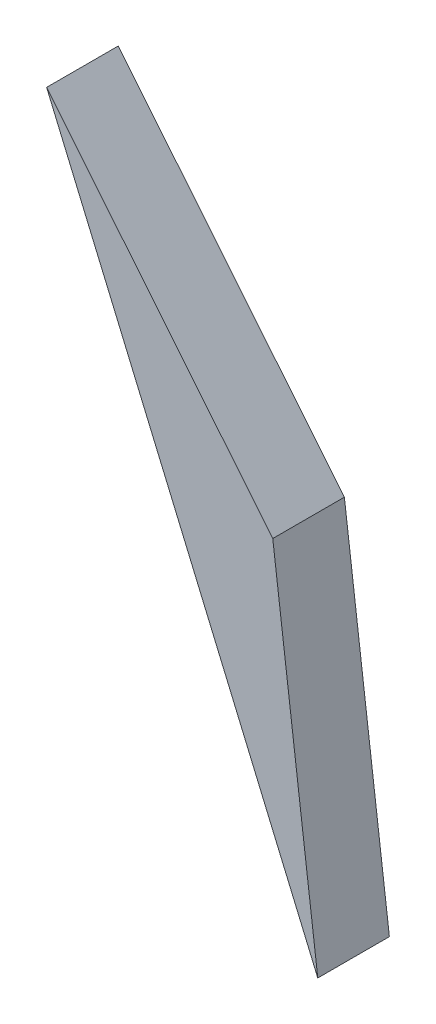
SolidWorks part; units mm, degrees
ref_plane "Plan de face" through (0, 0, 0) normal (0, 0, 1) x (1, 0, 0)
ref_plane "Plan de dessus" through (0, 0, 0) normal (0, 1, 0) x (1, 0, 0)
ref_plane "Plan de droite" through (0, 0, 0) normal (1, 0, 0) x (0, 0, -1)
sketch "Esquisse1" plane through (0, 0, 0) normal (0, 0, 1) x (1, 0, 0)
  line L0 (-12.3425, 10.4024) -> (-0.9839, -16.2277)
  line L1 (-0.9839, -16.2277) -> (-2.8693, -1.2277)
  line L2 (-2.8693, -1.2277) -> (-12.3425, 10.4024)
  line L3 (-64.2396, 74.1157) -> (-2.326, -1.8946) construction
  line L4 (5.5403, -68.1325) -> (-2.9766, -0.3741) construction
  point P3 (3.8602, 0)
  point P8 (-12.5461, 10.6524)
  point P9 (0, -15.5685)
  dimension "D1" = 15
  dimension "D2" = 15
extrude "Boss.-Extru.1" add sketch "Esquisse1" along normal blind 3
